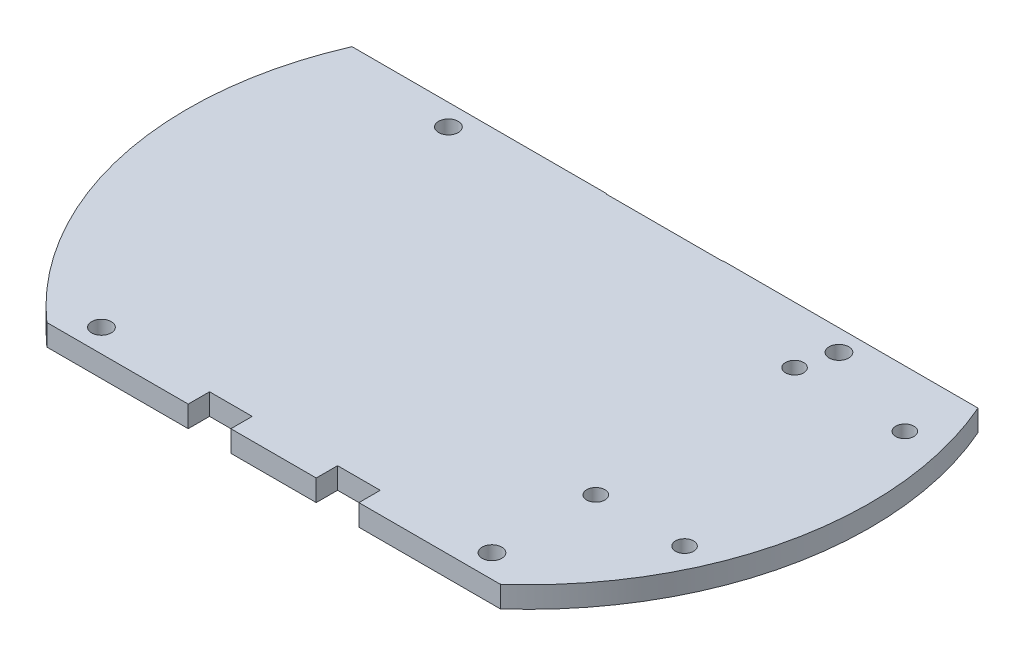
SolidWorks part; units mm, degrees
ref_plane "Front Plane" through (0, 0, 0) normal (0, 0, 1) x (1, 0, 0)
ref_plane "Top Plane" through (0, 0, 0) normal (0, 1, 0) x (1, 0, 0)
ref_plane "Right Plane" through (0, 0, 0) normal (1, 0, 0) x (0, 0, -1)
sketch "Sketch1" plane through (0, 0, 0) normal (0, 1, 0) x (1, 0, 0)
  circle A0 centre (0, 0) radius 50.8
extrude "Boss-Extrude1" add sketch "Sketch1" along normal blind 3.175
sketch "Sketch2" plane through (0, 3.175, 0) normal (0, 1, 0) x (1, 0, 0)
  line L0 (-50.8, 0) -> (50.8, 0) construction
  line L1 (-53.1411, 55.7151) -> (61.7467, 55.7151)
  line L2 (-53.1411, 55.7151) -> (-53.1411, 37.9781)
  line L3 (-53.1411, 37.9781) -> (-17.4664, 37.9781)
  line L4 (61.7467, 55.7151) -> (61.7467, 37.9781)
  line L5 (61.7467, -55.7151) -> (61.7467, -37.9781)
  line L6 (-53.1411, -37.9781) -> (61.7467, -37.9781)
  line L7 (-53.1411, -55.7151) -> (-53.1411, -37.9781)
  line L8 (-53.1411, -55.7151) -> (61.7467, -55.7151)
  line L9 (17.4664, 37.9781) -> (61.7467, 37.9781)
  line L10 (-36.7704, 37.9781) -> (-36.7704, 36.5923) construction
  line L11 (-17.4664, 37.9781) -> (-17.4664, 20.1981) construction
  line L12 (-17.4664, 20.1981) -> (17.4664, 20.1981) construction
  line L13 (17.4664, 37.9781) -> (17.4664, 20.1981) construction
  line L14 (0, 50.8) -> (0, 0) construction
  line L15 (36.7704, 37.9781) -> (36.7704, 36.5923) construction
  line L16 (0, 37.9781) -> (0, 20.1981) construction
  line L17 (-12.7, 37.9781) -> (12.7, 37.9781) construction
  line L18 (-12.7, 37.9781) -> (-12.7, 20.1981) construction
  line L19 (-12.7, 20.1981) -> (12.7, 20.1981) construction
  line L20 (12.7, 37.9781) -> (12.7, 20.1981) construction
  line L21 (0, 25.2781) -> (0, 20.1981) construction
  line L22 (-7.9756, 20.1981) -> (7.9756, 20.1981) construction
  line L26 (-8.5971, 20.1981) -> (8.5971, 20.1981)
  circle A0 centre (0, 0) radius 50.8 construction
  spline S0 degree 2 poles (-17.4664, 37.9781) (-17.0381, 26.7143) (-8.5971, 20.1981) knots 0 0 0 1 1 1
  spline S1 degree 2 poles (17.4664, 37.9781) (17.0381, 26.7143) (8.5971, 20.1981) knots 0 0 0 1 1 1
  dimension "D1" = 19.304
  dimension "D3" = 17.78
  dimension "D4" = 25.4
  dimension "D5" = 0
  dimension "D8" = 0
extrude "Cut-Extrude1" cut sketch "Sketch2" against normal blind 3.175
sketch "Sketch4" plane through (0, 3.175, 0) normal (0, 1, 0) x (1, 0, 0)
  line L0 (0, 20.1981) -> (0, -37.9781) construction
  line L1 (-8.5971, 20.1981) -> (8.5971, 20.1981) construction
  line L2 (33.7388, -37.9781) -> (-33.7388, -37.9781) construction
sketch "Sketch5" plane through (0, 0, 0) normal (0, -1, 0) x (1, 0, 0)
  line L0 (50.8, 0) -> (-52.1123, 0) construction
  circle A0 centre (0, 0) radius 50.8 construction
sketch "Sketch6" plane through (0, 3.175, 0) normal (0, 1, 0) x (1, 0, 0)
  circle A0 centre (-29.0576, 17.1018) radius 1.4605
  circle A1 centre (29.0576, 17.1018) radius 1.4605
  circle A2 centre (29.0576, -34.5364) radius 1.4605
  circle A3 centre (-29.0576, -34.5364) radius 1.4605
extrude "Cut-Extrude2" cut sketch "Sketch6" against normal blind 3.175
sketch "Sketch7" plane through (0, 0, 0) normal (0, -1, 0) x (1, 0, 0)
  line L3 (-63.0504, -48.8018) -> (57.7806, -48.8018)
  line L4 (-63.0504, -48.8018) -> (-63.0504, -20.2751)
  line L5 (-63.0504, -20.2751) -> (57.7806, -20.2751)
  line L6 (57.7806, -48.8018) -> (57.7806, -20.2751)
extrude "Cut-Extrude3" cut sketch "Sketch7" against normal blind 3.175
sketch "Sketch8" plane through (0, 0, 0) normal (0, -1, 0) x (1, 0, 0)
  line L0 (33.7388, 37.9781) -> (-33.7388, 37.9781) construction
  line L1 (-6.35, 37.9781) -> (-12.7, 37.9781)
  line L2 (-6.35, 37.9781) -> (-6.35, 34.8031)
  line L3 (-6.35, 34.8031) -> (-12.7, 34.8031)
  line L4 (-12.7, 37.9781) -> (-12.7, 34.8031)
  line L5 (0, -20.1981) -> (0, 37.9781) construction
  line L6 (0, 37.9781) -> (0, 15.0261) construction
  line L7 (12.7, 37.9781) -> (12.7, 34.8031)
  line L8 (6.35, 34.8031) -> (12.7, 34.8031)
  line L9 (6.35, 37.9781) -> (6.35, 34.8031)
  line L10 (6.35, 37.9781) -> (12.7, 37.9781)
  dimension "D1" = 6.35
  dimension "D2" = 6.35
  dimension "D3" = 3.175
extrude "Cut-Extrude4" cut sketch "Sketch8" against normal blind 3.175
sketch "Sketch9" plane through (0, 3.175, 0) normal (0, 1, 0) x (1, 0, 0)
  circle A0 centre (27.7254, 11.8281) radius 1.3462
  circle A1 centre (44.1338, 11.8281) radius 1.3462
  circle A2 centre (42.5336, -19.3504) radius 1.3462
  circle A3 centre (29.3256, -19.3504) radius 1.3462
extrude "Cut-Extrude5" cut sketch "Sketch9" against normal blind 3.175
